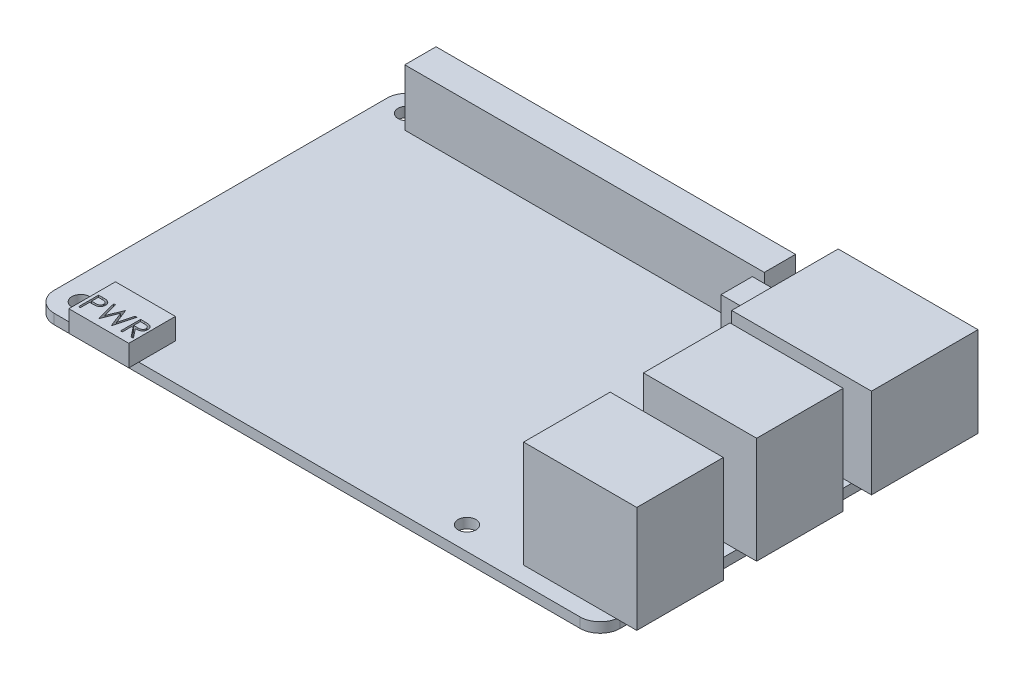
SolidWorks part; units mm, degrees
ref_plane "Front Plane" through (0, 0, 0) normal (0, 0, 1) x (1, 0, 0)
ref_plane "Top Plane" through (0, 0, 0) normal (0, 1, 0) x (1, 0, 0)
ref_plane "Right Plane" through (0, 0, 0) normal (1, 0, 0) x (0, 0, -1)
sketch "Sketch1" plane through (0, 0, 0) normal (0, 1, 0) x (1, 0, 0)
  line L0 (3.5, 52.5) -> (61.5, 52.5) construction
  line L1 (0, 0) -> (85, 0)
  line L2 (0, 0) -> (0, 56)
  line L3 (0, 56) -> (85, 56)
  line L4 (85, 0) -> (85, 56)
  line L5 (61.5, 52.5) -> (61.5, 3.5) construction
  line L6 (61.5, 3.5) -> (3.5, 3.5) construction
  line L7 (3.5, 3.5) -> (3.5, 52.5) construction
  circle A0 centre (3.5, 52.5) radius 1.35
  circle A1 centre (3.5, 3.5) radius 1.35
  circle A2 centre (61.5, 3.5) radius 1.35
  circle A3 centre (61.5, 52.5) radius 1.35
  point P13 (0, 0)
  dimension "D5" = 2.7
  dimension "D6" = 3.5
  dimension "D7" = 3.5
  dimension "D1" = 85
  dimension "D2" = 56
  dimension "D3" = 58
  dimension "D4" = 49
extrude "Boss-Extrude1" add sketch "Sketch1" along normal blind 1.5
fillet "Fillet1" radius 3 4 edges at (85, 0.75, -56) (85, 0.75, 0) (0, 0.75, -56) (0, 0.75, 0)
sketch "Sketch2" plane through (0, 1.5, 0) normal (0, 1, 0) x (1, 0, 0)
  line L0 (3, 0) -> (82, 0) construction
  line L1 (88, 20.5) -> (71, 20.5)
  line L2 (88, 20.5) -> (88, 33.5)
  line L3 (88, 33.5) -> (71, 33.5)
  line L4 (71, 20.5) -> (71, 33.5)
  line L5 (88, 2.5) -> (71, 2.5)
  line L6 (88, 2.5) -> (88, 15.5)
  line L7 (88, 15.5) -> (71, 15.5)
  line L8 (71, 2.5) -> (71, 15.5)
  line L9 (85, 3) -> (85, 53) construction
  point P8 (88, 9)
  point P11 (88, 27)
  dimension "D1" = 17
  dimension "D2" = 13
  dimension "D3" = 9
  dimension "D4" = 27
  dimension "D5" = 3
extrude "Boss-Extrude2" add sketch "Sketch2" along normal blind 16
sketch "Sketch3" plane through (0, 1.5, 0) normal (0, 1, 0) x (1, 0, 0)
  line L0 (88, 20.5) -> (88, 33.5) construction
  line L1 (88, 37.75) -> (67, 37.75)
  line L2 (88, 37.75) -> (88, 53.75)
  line L3 (88, 53.75) -> (67, 53.75)
  line L4 (67, 37.75) -> (67, 53.75)
  line L5 (3, 0) -> (82, 0) construction
  point P6 (88, 45.75)
  dimension "D1" = 21
  dimension "D2" = 16
  dimension "D3" = 45.75
extrude "Boss-Extrude3" add sketch "Sketch3" along normal blind 13.5
sketch "Sketch4" plane through (0, 1.5, 0) normal (0, 1, 0) x (1, 0, 0)
  line L0 (61.5, 52.5) -> (61.5, 48.71) construction
  line L1 (5.5, 54.85) -> (59.5, 54.85)
  line L2 (5.5, 54.85) -> (5.5, 50.15)
  line L3 (5.5, 50.15) -> (59.5, 50.15)
  line L4 (59.5, 54.85) -> (59.5, 50.15)
  line L5 (59.15, 48.71) -> (63.85, 48.71)
  line L6 (59.15, 48.71) -> (59.15, 44.01)
  line L7 (59.15, 44.01) -> (63.85, 44.01)
  line L8 (63.85, 48.71) -> (63.85, 44.01)
  line L9 (3.5, 52.5) -> (61.5, 52.5) construction
  point P11 (63.85, 46.36)
  point P13 (32.5, 52.5)
  point P15 (32.5, 54.85)
  point P16 (5.5, 52.5)
  dimension "D1" = 6.14
  dimension "D2" = 54
  dimension "D3" = 4.7
  dimension "D4" = 4.7
extrude "Boss-Extrude4" add sketch "Sketch4" along normal blind 8.5
sketch "Sketch5" plane through (0, 1.5, 0) normal (0, 1, 0) x (1, 0, 0)
  line L0 (3, 0) -> (82, 0) construction
  line L1 (6.7, -1.5) -> (15.7, -1.5)
  line L2 (6.7, -1.5) -> (6.7, 5.5)
  line L3 (6.7, 5.5) -> (15.7, 5.5)
  line L4 (15.7, -1.5) -> (15.7, 5.5)
  circle A0 centre (3.5, 3.5) radius 1.35 construction
  point P8 (11.2, -1.5)
  dimension "D4" = 7.7
  dimension "D1" = 9
  dimension "D2" = 7
  dimension "D3" = 1.5
extrude "Boss-Extrude5" add sketch "Sketch5" along normal blind 3.2
sketch "Sketch6" plane through (0, 4.7, 0) normal (0, 1, 0) x (1, 0, 0)
  line L0 (6.7, -0.5) -> (15.7, -0.5) construction
  line L1 (6.7, 5.5) -> (6.7, -1.5) construction
  line L2 (15.7, -1.5) -> (15.7, 5.5) construction
  line L3 (6.7, -1.5) -> (15.7, -1.5) construction
  text T0 "PWR" font "Century Gothic" height 3
  dimension "D1" = 1
extrude "Cut-Extrude1" cut sketch "Sketch6" against normal blind 1
